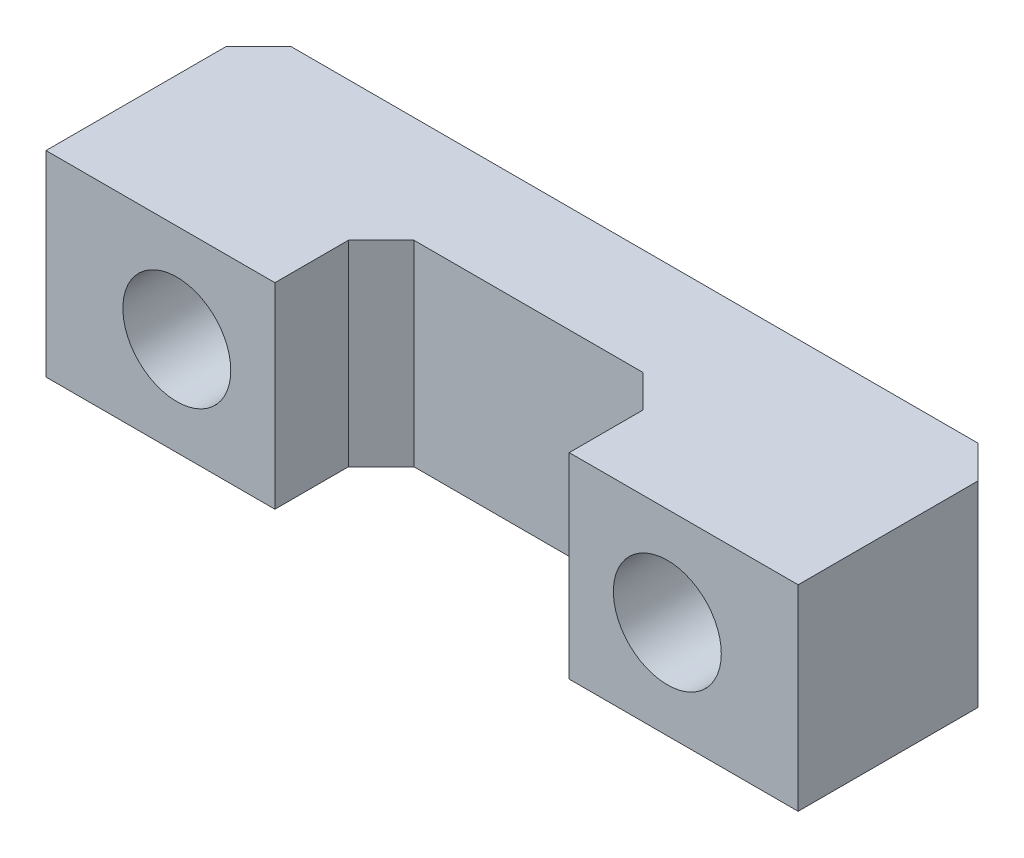
SolidWorks part; units mm, degrees
ref_plane "前视基准面" through (0, 0, 0) normal (0, 0, 1) x (1, 0, 0)
ref_plane "上视基准面" through (0, 0, 0) normal (0, 1, 0) x (1, 0, 0)
ref_plane "右视基准面" through (0, 0, 0) normal (1, 0, 0) x (0, 0, -1)
sketch "草图1" plane through (0, 0, 0) normal (0, 1, 0) x (1, 0, 0)
  line L1 (-11.5, 0.5) -> (-11.5, 6)
  line L3 (11.5, 0.5) -> (11.5, 6)
  line L4 (10.5, 7) -> (-10.5, 7)
  line L5 (-4.5, 2.75) -> (-4.5, 0.5)
  line L6 (-3.5, 3.75) -> (-4.5, 2.75)
  line L7 (3.5, 3.75) -> (-3.5, 3.75)
  line L8 (3.5, 3.75) -> (4.5, 2.75)
  line L9 (4.5, 0.5) -> (4.5, 2.75)
  line L10 (-11.5, 0.5) -> (-4.5, 0.5)
  line L11 (4.5, 0.5) -> (11.5, 0.5)
  line L12 (-11.5, 6) -> (-10.5, 7)
  line L13 (11.5, 6) -> (10.5, 7)
  point P2 (-11.5, 7)
  point P5 (11.5, 7)
  point P15 (0, 3.75)
  dimension "D1" = 4.5
  dimension "D2" = 4.5
  dimension "D5" = 7
  dimension "D6" = 7
  dimension "D7" = 6.5
  dimension "D8" = 2.25
extrude "凸台-拉伸1" add sketch "草图1" along normal blind 6
sketch "草图2" plane through (0, 0, -0.5) normal (0, 0, 1) x (1, 0, 0)
  circle A0 centre (-7.5, 3) radius 1.65
  circle A1 centre (7.5, 3) radius 1.65
extrude "切除-拉伸1" cut sketch "草图2" against normal blind 8
